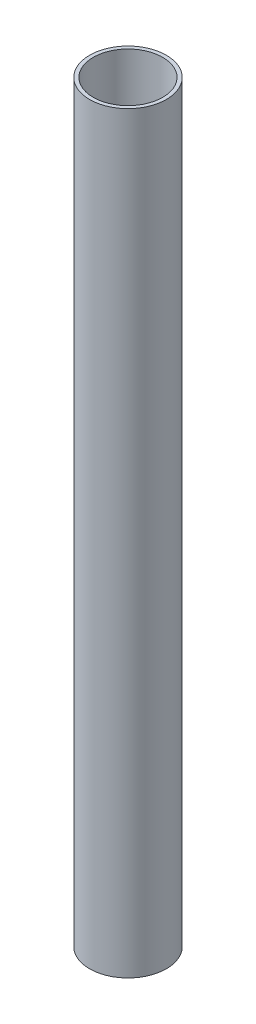
SolidWorks part; units mm, degrees
ref_plane "Front Plane" through (0, 0, 0) normal (0, 0, 1) x (1, 0, 0)
ref_plane "Top Plane" through (0, 0, 0) normal (0, 1, 0) x (1, 0, 0)
ref_plane "Right Plane" through (0, 0, 0) normal (1, 0, 0) x (0, 0, -1)
sketch "Sketch1" plane through (0, 0, 0) normal (0, 1, 0) x (1, 0, 0)
  circle A0 centre (0, 0) radius 21
  circle A1 centre (0, 0) radius 19
extrude "Boss-Extrude1" add sketch "Sketch1" along normal blind 412
